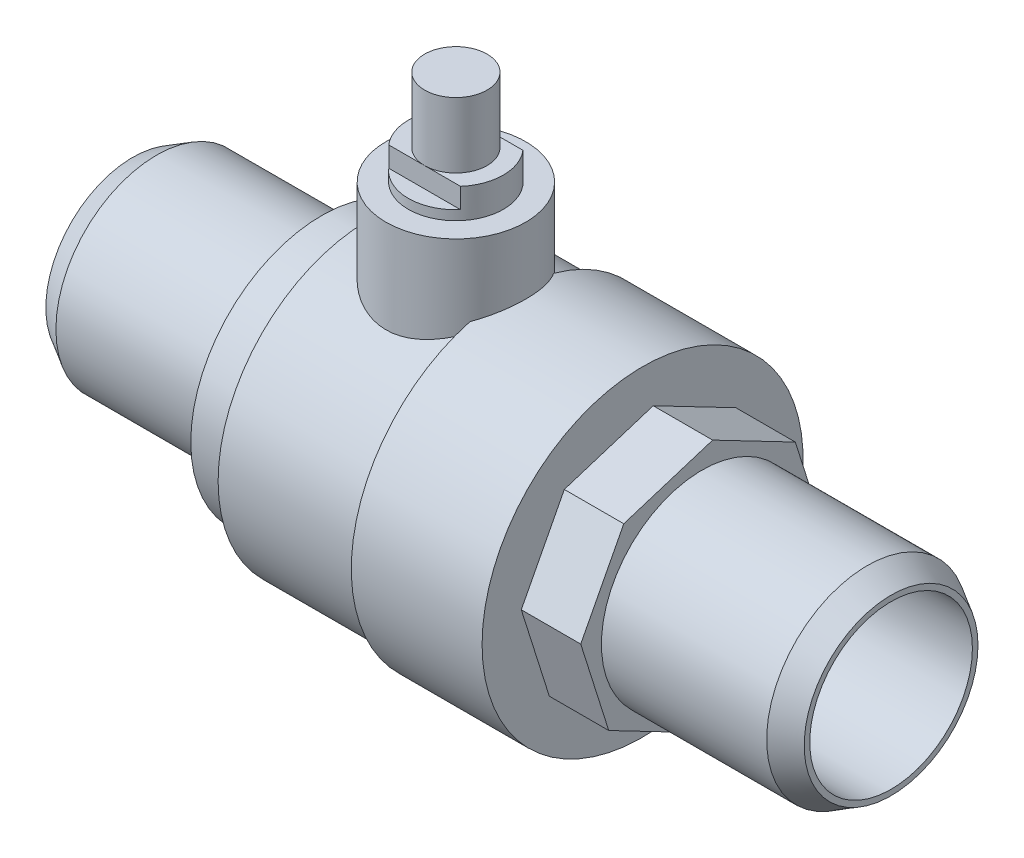
SolidWorks part; units mm, degrees
material "Brass"
ref_plane "Front Plane" through (0, 0, 0) normal (0, 0, 1) x (1, 0, 0)
ref_plane "Top Plane" through (0, 0, 0) normal (0, 1, 0) x (1, 0, 0)
ref_plane "Right Plane" through (0, 0, 0) normal (1, 0, 0) x (0, 0, -1)
sketch "Sketch1" plane through (0, 0, 0) normal (1, 0, 0) x (0, 0, -1)
  circle A0 centre (0, 0) radius 8.4646
extrude "Boss-Extrude1" add sketch "Sketch1" along normal mid plane 63.78
ref_plane "Plane1" through (15.99, 0, 0) normal (1, 0, 0) x (0, 0, -1)
sketch "Sketch5" plane through (15.99, 0, 0) normal (1, 0, 0) x (0, 0, -1)
  line L1 (7.8451, 6.5828) -> (0.8926, 10.2021)
  line L2 (0.8926, 10.2021) -> (-6.5828, 7.8451)
  line L3 (-6.5828, 7.8451) -> (-10.2021, 0.8926)
  line L4 (-10.2021, 0.8926) -> (-7.8451, -6.5828)
  line L5 (-7.8451, -6.5828) -> (-0.8926, -10.2021)
  line L6 (-0.8926, -10.2021) -> (6.5828, -7.8451)
  line L7 (6.5828, -7.8451) -> (10.2021, -0.8926)
  line L8 (10.2021, -0.8926) -> (7.8451, 6.5828)
  circle A0 centre (0, 0) radius 9.4615 construction
extrude "Boss-Extrude3" add sketch "Sketch5" against normal blind 5
sketch "Sketch6" plane through (10.99, 0, 0) normal (-1, 0, 0) x (0, 0, 1)
  circle A0 centre (0, 0) radius 13.5
extrude "Boss-Extrude4" add sketch "Sketch6" along normal blind 11
sketch "Sketch7" plane through (-0.01, 0, 0) normal (-1, 0, 0) x (0, 0, 1)
  circle A0 centre (0, 0) radius 12.7
extrude "Boss-Extrude5" add sketch "Sketch7" along normal blind 12
sketch "Sketch8" plane through (-12.01, 0, 0) normal (-1, 0, 0) x (0, 0, 1)
  circle A0 centre (0, 0) radius 11
extrude "Boss-Extrude6" add sketch "Sketch8" along normal blind 4
sketch "Sketch9" plane through (0, 0, 0) normal (0, 1, 0) x (1, 0, 0)
  line L0 (-31.89, 0) -> (-4.715, 0) construction
  line L1 (-31.89, 8.4646) -> (-31.89, -8.4646) construction
  circle A0 centre (-4.715, 0) radius 5.875
extrude "Boss-Extrude7" add sketch "Sketch9" along normal blind 19.1
sketch "Sketch10" plane through (0, 19.1, 0) normal (0, 1, 0) x (1, 0, 0)
  circle A0 centre (-4.715, 0) radius 4
extrude "Boss-Extrude8" add sketch "Sketch10" along normal blind 2.5
sketch "Sketch11" plane through (0, 21.6, 0) normal (0, 1, 0) x (1, 0, 0)
  line L1 (-12.1263, -2.625) -> (2.6963, -2.625)
  line L2 (-12.1263, -2.625) -> (-12.1263, 2.625)
  line L3 (-12.1263, 2.625) -> (2.6963, 2.625)
  line L4 (2.6963, -2.625) -> (2.6963, 2.625)
  line L5 (-12.1263, -2.625) -> (2.6963, 2.625) construction
  line L6 (-12.1263, 2.625) -> (2.6963, -2.625) construction
  circle A0 centre (-4.715, 0) radius 2.625 construction
extrude "Cut-Extrude4" cut sketch "Sketch11" against normal blind 1.7 flip side to cut
sketch "Sketch12" plane through (0, 21.6, 0) normal (0, 1, 0) x (1, 0, 0)
  circle A0 centre (-4.715, 0) radius 2.625
extrude "Boss-Extrude9" add sketch "Sketch12" along normal blind 5.5
sketch "Sketch2" plane through (0, 0, 0) normal (1, 0, 0) x (0, 0, -1)
  circle A0 centre (0, 0) radius 6.84
extrude "Cut-Extrude3" cut sketch "Sketch2" against normal through all both and the other way through all
chamfer "Chamfer1" distance 2 angle 30 2 edges at (-31.89, 0, -8.4646) (31.89, 0, -8.4646)
